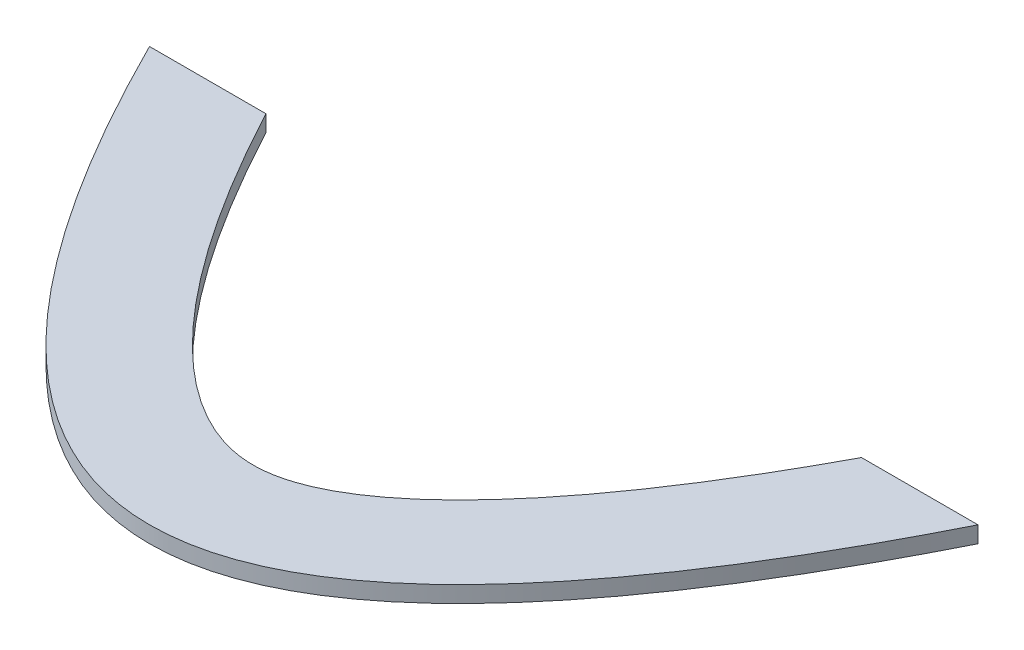
SolidWorks part; units mm, degrees
ref_plane "Front Plane" through (0, 0, 0) normal (0, 0, 1) x (1, 0, 0)
ref_plane "Top Plane" through (0, 0, 0) normal (0, 1, 0) x (1, 0, 0)
ref_plane "Right Plane" through (0, 0, 0) normal (1, 0, 0) x (0, 0, -1)
sketch "Sketch2" plane through (0, 0, 0) normal (0, 1, 0) x (1, 0, 0)
  line L0 (-80, 80) -> (-57.4998, 80)
  line L1 (80, 80) -> (57.4998, 80)
  spline S0 degree 2 poles (-90.0959, 101.4658) (0, -101.4658) (90.0959, 101.4658) knots 0 0 0 1 1 1 construction
  spline S1 degree 2 poles (-80, 80) (0, -80) (80, 80) knots 0.056028 0.056028 0.056028 0.943972 0.943972 0.943972
  spline S2 degree 1 poles (-62.1115, 88.9443) (62.1115, 88.9443) knots 0 0 1 1 construction
  spline S3 degree 3 poles (-62.1115, 88.9443) (-61.7163, 88.1539) (-60.9168, 86.5673) (-59.331, 83.4702) (-57.351, 79.6959) (-54.9867, 75.3369) (-51.8486, 69.7473) (-47.9568, 63.1815) (-43.3467, 55.9802) (-38.8102, 49.4616) (-32.8823, 41.6849) (-25.7482, 33.6868) (-17.8453, 26.8212) (-10.8707, 22.5283) (-5.0063, 20.3968) (0, 19.8016) (5.0063, 20.3968) (10.8707, 22.5283) (17.8453, 26.8212) (25.7482, 33.6868) (32.8823, 41.6849) (38.8102, 49.4616) (43.3467, 55.9802) (47.9568, 63.1815) (51.8486, 69.7473) (54.9867, 75.3369) (57.351, 79.6959) (59.331, 83.4702) (60.9168, 86.5673) (61.7163, 88.1539) (62.1115, 88.9443) knots 0.056028 0.056028 0.056028 0.056028 0.062965 0.069903 0.083777 0.097651 0.111525 0.139273 0.167021 0.19477 0.222518 0.278014 0.333511 0.389007 0.444504 0.5 0.555496 0.610993 0.666489 0.721986 0.777482 0.80523 0.832979 0.860727 0.888475 0.902349 0.916223 0.930097 0.937035 0.943972 0.943972 0.943972 0.943972 only from (-57.4998, 80) to (57.4998, 80)
  dimension "D1" = 20
extrude "Boss-Extrude2" add sketch "Sketch2" along normal blind 3.175 contours L0 S3 L1 S1
